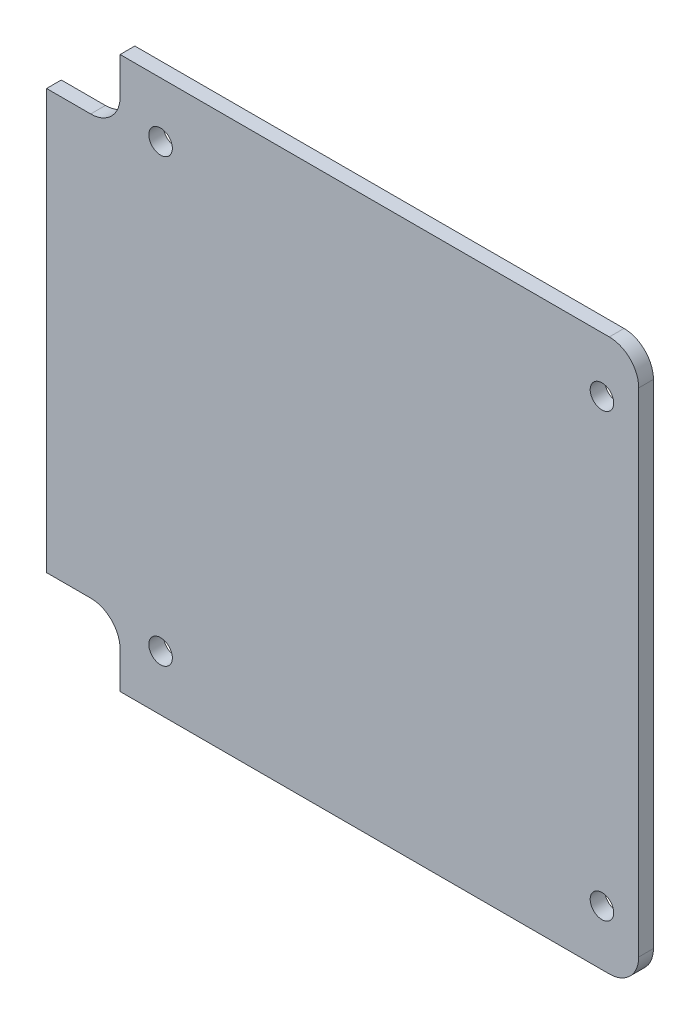
SolidWorks part; units mm, degrees
ref_plane "正面" through (0, 0, 0) normal (0, 0, 1) x (1, 0, 0)
ref_plane "平面" through (0, 0, 0) normal (0, 1, 0) x (1, 0, 0)
ref_plane "右側面" through (0, 0, 0) normal (1, 0, 0) x (0, 0, -1)
sketch "ｽｹｯﾁ1" plane through (0, 0, 0) normal (0, 0, 1) x (1, 0, 0)
  line L1 (-40.25, 37.5) -> (40.25, 37.5)
  line L2 (-40.25, 37.5) -> (-40.25, -37.5)
  line L3 (-40.25, -37.5) -> (40.25, -37.5)
  line L4 (40.25, 37.5) -> (40.25, -37.5)
  line L5 (-40.25, 37.5) -> (-30.25, 37.5)
  line L6 (-40.25, 37.5) -> (-40.25, 28.5)
  line L7 (-40.25, 28.5) -> (-30.25, 28.5)
  line L8 (-30.25, 37.5) -> (-30.25, 28.5)
  line L9 (-40.25, -37.5) -> (-30.25, -37.5)
  line L10 (-40.25, -37.5) -> (-40.25, -28.5)
  line L11 (-40.25, -28.5) -> (-30.25, -28.5)
  line L12 (-30.25, -37.5) -> (-30.25, -28.5)
  circle A0 centre (35.25, -30) radius 1.6
  circle A1 centre (35.25, 30) radius 1.6
  circle A2 centre (-24.75, 30) radius 1.6
  circle A3 centre (-24.75, -30) radius 1.6
  dimension "D9" = 3.2
  dimension "D10" = 3.2
  dimension "D15" = 3.2
  dimension "D18" = 3.2
  dimension "D1" = 80.5
  dimension "D2" = 75
  dimension "D3" = 37.5
  dimension "D4" = 40.25
  dimension "D5" = 10
  dimension "D6" = 10
  dimension "D7" = 9
  dimension "D8" = 9
  dimension "D11" = 30
  dimension "D12" = 5
  dimension "D13" = 5
  dimension "D14" = 30
  dimension "D16" = 30
  dimension "D17" = 60
  dimension "D19" = 30
  dimension "D20" = 60
extrude "ﾎﾞｽ - 押し出し1" add sketch "ｽｹｯﾁ1" along normal blind 2 contours L12 L3 L4 L1 L8 L7 L2 L11 A3 A2 A1 A0
fillet "ﾌｨﾚｯﾄ1" radius 4 4 edges at (-30.25, 28.5, 1) (40.25, 37.5, 1) (40.25, -37.5, 1) (-30.25, -28.5, 1)
